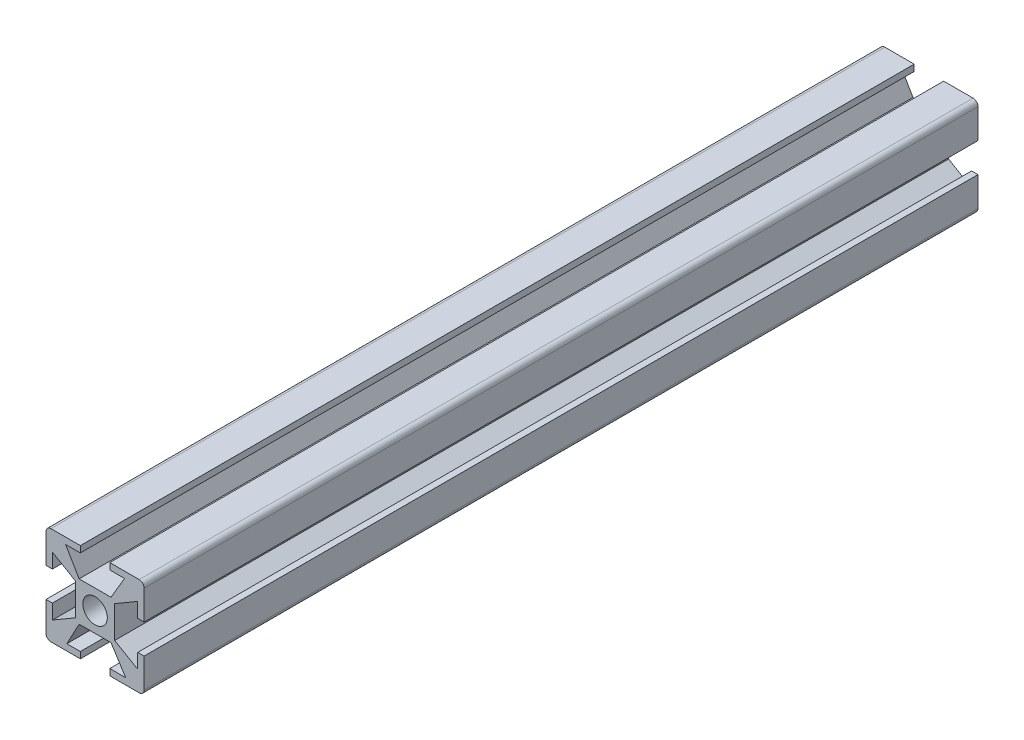
SolidWorks part; units mm, degrees
ref_plane "Alzado" through (0, 0, 0) normal (0, 0, 1) x (1, 0, 0)
ref_plane "Planta" through (0, 0, 0) normal (0, 1, 0) x (1, 0, 0)
ref_plane "Vista lateral" through (0, 0, 0) normal (1, 0, 0) x (0, 0, -1)
sketch "Croquis1" plane through (0, 0, 0) normal (0, 0, 1) x (1, 0, 0)
  line L0 (-3, 10) -> (3, 10)
  line L1 (-9, 10) -> (9, 10)
  line L2 (-10, 9) -> (-10, -9)
  line L3 (-9, -10) -> (9, -10)
  line L4 (10, 9) -> (10, -9)
  line L5 (-10, 10) -> (10, -10) construction
  line L6 (-10, -10) -> (10, 10) construction
  line L7 (-4, 4) -> (4, 4)
  line L8 (-4, 4) -> (-4, -4)
  line L9 (-4, -4) -> (4, -4)
  line L10 (4, 4) -> (4, -4)
  line L11 (-4, 4) -> (4, -4) construction
  line L12 (-4, -4) -> (4, 4) construction
  line L13 (3, 10) -> (3, 8.7)
  line L14 (-3.25, 4) -> (3.25, 4)
  line L15 (0, 10) -> (0, -10) construction
  line L16 (-10, 0) -> (10, 0) construction
  line L20 (-3, 10) -> (-3, 8.7)
  line L22 (3, -10) -> (3, -8.7)
  line L23 (-3, -10) -> (3, -10)
  line L24 (-3, -10) -> (-3, -8.7)
  line L25 (-5.75, -8.7) -> (-3, -8.7)
  line L26 (-5.75, -8.7) -> (-3.25, -4)
  line L27 (-3.25, -4) -> (3.25, -4)
  line L28 (6.25, -8.7) -> (3.25, -4)
  line L29 (3, -8.7) -> (6.25, -8.7)
  line L30 (-10, 3) -> (-10, -3)
  line L31 (-4, 3.25) -> (-4, -3.25)
  line L32 (-10, 3) -> (-8.7, 3)
  line L33 (-8.7, -6) -> (-8.7, -3)
  line L34 (-8.7, 6) -> (-4, 3.25)
  line L35 (-8.7, -6) -> (-4, -3.25)
  line L36 (-10, -3) -> (-8.7, -3)
  line L37 (-8.7, 3) -> (-8.7, 6)
  line L38 (8.7, -6) -> (4, -3.25)
  line L39 (4, 3.25) -> (4, -3.25)
  line L40 (8.7, 6) -> (4, 3.25)
  line L41 (8.7, 3) -> (8.7, 6)
  line L42 (10, 3) -> (8.7, 3)
  line L43 (10, 3) -> (10, -3)
  line L44 (10, -3) -> (8.7, -3)
  line L45 (8.7, -6) -> (8.7, -3)
  line L46 (-6, 8.7) -> (-3, 8.7)
  line L47 (-6, 8.7) -> (-3.25, 4)
  line L48 (6, 8.7) -> (3.25, 4)
  line L49 (3, 8.7) -> (6, 8.7)
  circle A0 centre (0, 0) radius 2.5
  arc A1 (-10, -9) -> (-9, -10) centre (-9, -9) ccw
  arc A2 (9, -10) -> (10, -9) centre (9, -9) ccw
  arc A3 (9, 10) -> (10, 9) centre (9, 9) cw
  arc A4 (-9, 10) -> (-10, 9) centre (-9, 9) ccw
  point P0 (0, 0)
  point P6 (0, 0)
  point P14 (0, 10)
  point P18 (0, 4)
  point P25 (0, 8.7)
  point P37 (-10, 0)
  point P40 (-4, 0)
  point P44 (-8.7, 0)
  point P56 (0, 8.7)
  dimension "D12" = 5
  dimension "D13" = 1
  dimension "D1" = 20
  dimension "D2" = 20
  dimension "D3" = 8
  dimension "D4" = 8
  dimension "D5" = 6
  dimension "D6" = 6.5
  dimension "D7" = 12
  dimension "D8" = 6.5
  dimension "D9" = 6
  dimension "D10" = 1.3
  dimension "D11" = 12
extrude "Saliente-Extruir4" add sketch "Croquis1" along normal blind 170 contours L1 A4 L2 L32 L37 L34 L8 L7 L47 L46 L20 | A3 L1 L13 L49 L48 L7 L10 L40 L41 L42 L4 | L3 A2 L4 L44 L45 L38 L10 L9 L28 L29 L22 | L2 A1 L3 L24 L25 L26 L9 L8 L35 L33 L36 | L10 L7 L8 L9 A0
